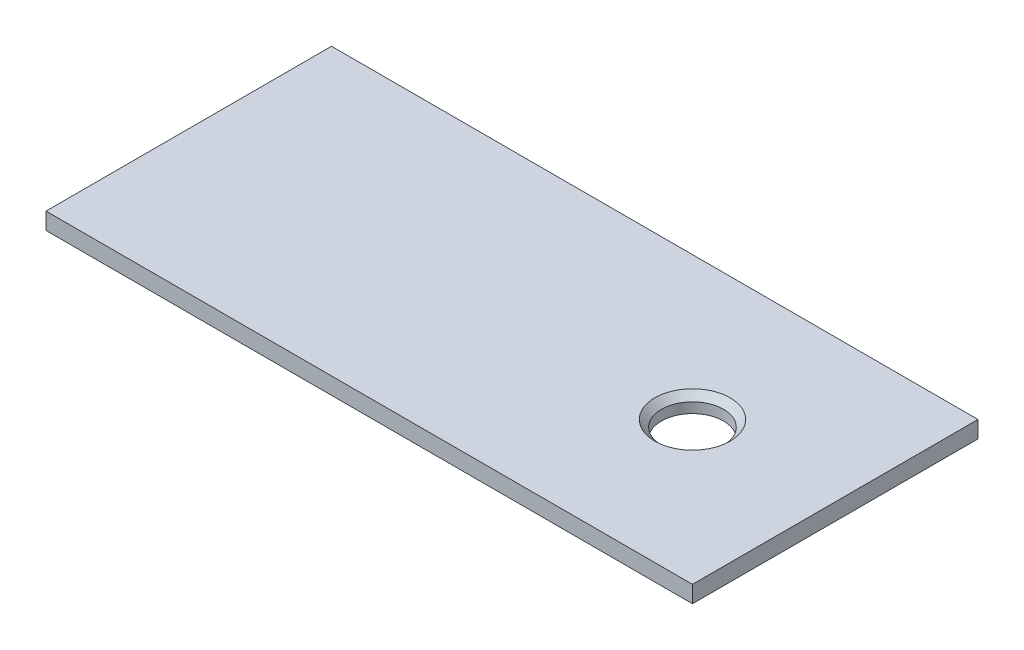
SolidWorks part; units mm, degrees
ref_plane "Front Plane" through (0, 0, 0) normal (0, 0, 1) x (1, 0, 0)
ref_plane "Top Plane" through (0, 0, 0) normal (0, 1, 0) x (1, 0, 0)
ref_plane "Right Plane" through (0, 0, 0) normal (1, 0, 0) x (0, 0, -1)
sketch "Sketch1" plane through (0, 0, 0) normal (0, 1, 0) x (1, 0, 0)
  line L1 (-60, -26.5) -> (60, -26.5)
  line L2 (-60, -26.5) -> (-60, 26.5)
  line L3 (-60, 26.5) -> (60, 26.5)
  line L4 (60, -26.5) -> (60, 26.5)
  line L5 (-60, -26.5) -> (60, 26.5) construction
  line L6 (-60, 26.5) -> (60, -26.5) construction
  point P0 (0, 0)
extrude "Boss-Extrude1" add sketch "Sketch1" along normal blind 3.125
hole_wizard "1/2-20 Tapped Hole1" positions "Sketch5" profile "Sketch3" tap size "1/2-20" standard "ANSI Inch"
sketch "Sketch5" plane through (0, 3.125, 0) normal (0, 1, 0) x (1, 0, 0)
  line L0 (60, -26.5) -> (60, 26.5) construction
  point P0 (33.5, 0)
  dimension "D1" = 26.5
sketch "Sketch3" plane through (33.5, 3.125, 0) normal (1, 0, 0) x (0, 0, 1)
  line L0 (0, 0) -> (0, 33.4576)
  line L1 (0, 33.4576) -> (5.7544, 30)
  line L2 (5.7544, 30) -> (5.7544, 1.2306)
  line L3 (5.7544, 1.2306) -> (6.985, 0)
  line L5 (6.985, 0) -> (0, 0)
  line L6 (-5.7544, 1.2306) -> (-6.985, 0) construction
  line L10 (0, 33.4576) -> (-5.7544, 30) construction
  line L11 (0, -6.35) -> (0, 107.95) construction
  dimension "Tap Drill Dia." = 11.5087
  dimension "Tap Drill Depth" = 30
  dimension "Near C'Sink Dia." = 13.97
  dimension "Near C'Sink Angle" = 90
  dimension "Drill Angle" = 118
cosmetic thread "Hole Thread1"
